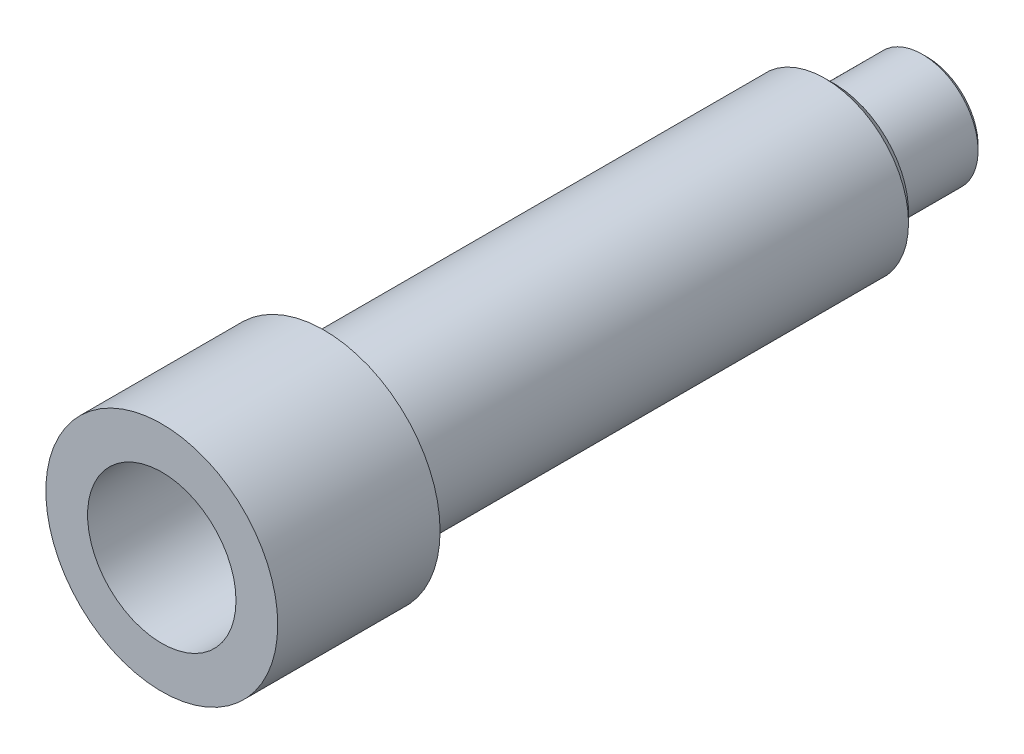
SolidWorks part; units mm, degrees
ref_plane "前视基准面" through (0, 0, 0) normal (0, 0, 1) x (1, 0, 0)
ref_plane "上视基准面" through (0, 0, 0) normal (0, 1, 0) x (1, 0, 0)
ref_plane "右视基准面" through (0, 0, 0) normal (1, 0, 0) x (0, 0, -1)
sketch "草图1" plane through (0, 0, 0) normal (0, 0, 1) x (1, 0, 0)
  circle A0 centre (0, 0) radius 12.5
  dimension "D1" = 25
extrude "凸台-拉伸1" add sketch "草图1" along normal blind 17.5
sketch "草图2" plane through (0, 0, 0) normal (0, 0, -1) x (-1, 0, 0)
  circle A0 centre (0, 0) radius 9
  dimension "D1" = 18
extrude "凸台-拉伸2" add sketch "草图2" along normal blind 55
sketch "草图3" plane through (0, 0, -55) normal (0, 0, -1) x (-1, 0, 0)
  circle A0 centre (0, 0) radius 6
  dimension "D1" = 12
extrude "凸台-拉伸3" add sketch "草图3" along normal blind 10
chamfer "倒角1" distance 0.5 angle 45 1 edges at (-6, 0, -65)
sketch "草图4" plane through (0, 0, -65) normal (0, 0, -1) x (-1, 0, 0)
  circle A0 centre (0, 0) radius 5
  dimension "D1" = 10
extrude "切除-拉伸1" cut sketch "草图4" against normal blind 139
chamfer "倒角2" distance 1 angle 45 1 edges at (-9, 0, -55)
sketch "草图5" plane through (0, 0, 17.5) normal (0, 0, 1) x (1, 0, 0)
  circle A0 centre (0, 0) radius 8
  dimension "D1" = 16
extrude "切除-拉伸2" cut sketch "草图5" against normal blind 12
